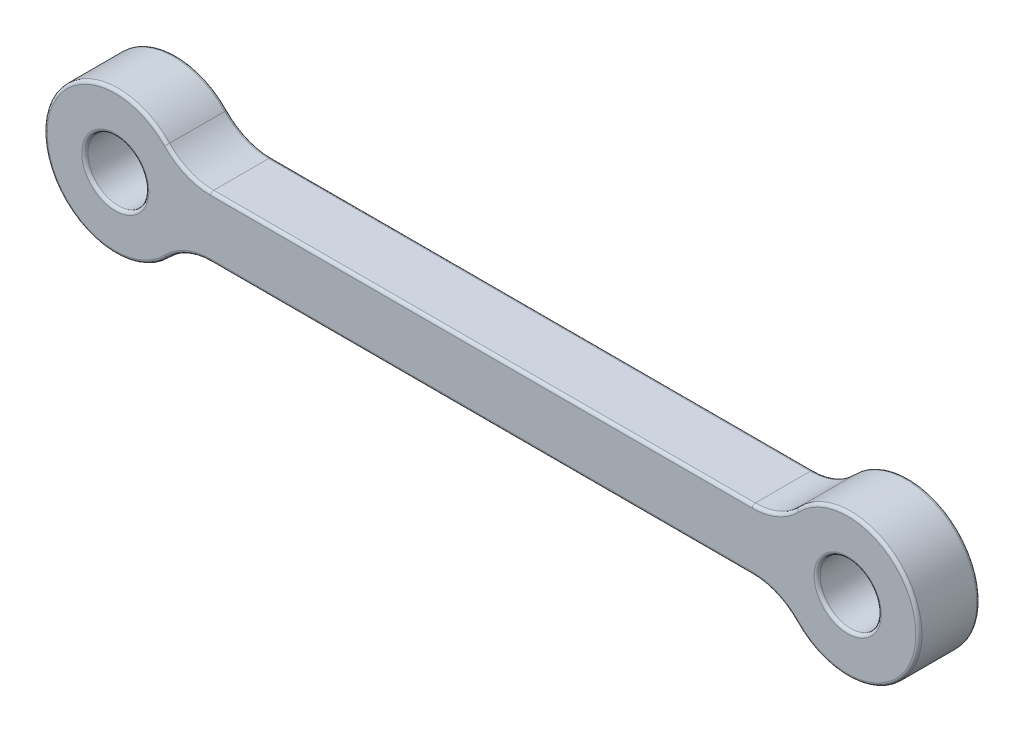
SolidWorks part; units mm, degrees
ref_plane "Front Plane" through (0, 0, 0) normal (0, 0, 1) x (1, 0, 0)
ref_plane "Top Plane" through (0, 0, 0) normal (0, 1, 0) x (1, 0, 0)
ref_plane "Right Plane" through (0, 0, 0) normal (1, 0, 0) x (0, 0, -1)
sketch "Sketch1" plane through (0, 0, 0) normal (0, 0, 1) x (1, 0, 0)
  line L0 (0, 0) -> (36, 0) construction
  line L1 (0, 3.5) -> (36, 3.5) construction
  line L2 (0, -3.5) -> (36, -3.5) construction
  line L3 (18, 0) -> (18, -3.5) construction
  line L5 (3.1623, -1.5) -> (32.8377, -1.5)
  line L6 (3.1623, -1.5) -> (3.1623, 1.5) construction
  line L7 (3.1623, 1.5) -> (32.8377, 1.5)
  line L8 (32.8377, -1.5) -> (32.8377, 1.5) construction
  line L9 (3.1623, -1.5) -> (32.8377, 1.5) construction
  line L10 (3.1623, 1.5) -> (32.8377, -1.5) construction
  arc A0 (0, 3.5) -> (0, -3.5) centre (0, 0) ccw construction
  arc A1 (36, -3.5) -> (36, 3.5) centre (36, 0) ccw construction
  circle A2 centre (0, 0) radius 3.5
  circle A3 centre (0, 0) radius 1.5
  circle A4 centre (36, 0) radius 1.5
  circle A5 centre (36, 0) radius 3.5
  point P3 (18, 0)
  dimension "D3" = 3
  dimension "D1" = 7
  dimension "D2" = 36
  dimension "D4" = 3
extrude "Boss-Extrude1" add sketch "Sketch1" along normal mid plane 3 contours A2 A3 | L5 A5 L7 A2 | A5 A4
fillet "Fillet1" radius 3 4 edges at (3.1623, -1.5, 0) (32.8377, -1.5, 0) (32.8377, 1.5, 0) (3.1623, 1.5, 0)
fillet "Fillet2" radius 0.15 20 edges at (37.5, 0, 1.5) (37.5, 0, -1.5) (1.5, 0, 1.5) (1.5, 0, -1.5) (3.5137, -1.7404, 1.5) (3.5137, -1.7404, -1.5) (18, -1.5, 1.5) (18, -1.5, -1.5) (32.4863, -1.7404, 1.5) (32.4863, -1.7404, -1.5) (39.5, 0, 1.5) (39.5, 0, -1.5) (32.4863, 1.7404, 1.5) (32.4863, 1.7404, -1.5) (18, 1.5, 1.5) (18, 1.5, -1.5) (3.5137, 1.7404, 1.5) (3.5137, 1.7404, -1.5) (-3.5, 0, -1.5) (-3.5, 0, 1.5)
